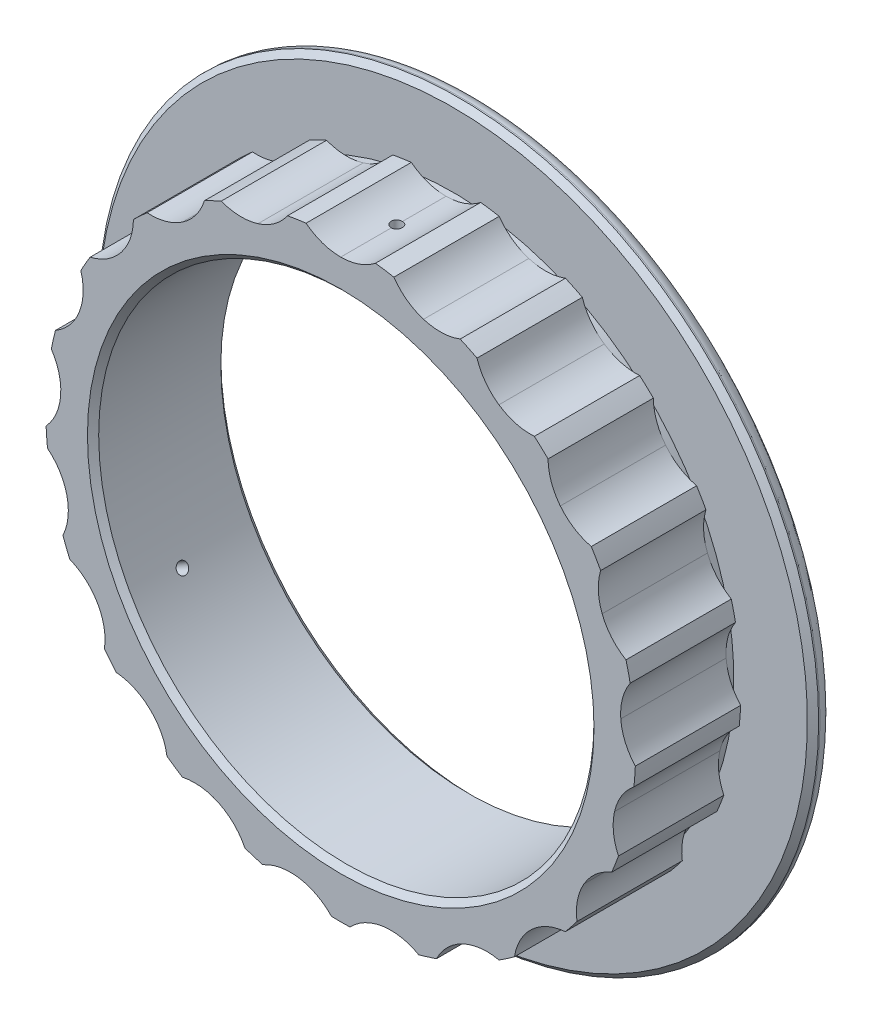
SolidWorks part; units mm, degrees
ref_plane "Front Plane" through (0, 0, 0) normal (0, 0, 1) x (1, 0, 0)
ref_plane "Top Plane" through (0, 0, 0) normal (0, 1, 0) x (1, 0, 0)
ref_plane "Right Plane" through (0, 0, 0) normal (1, 0, 0) x (0, 0, -1)
sketch "Sketch1" plane through (0, 0, 0) normal (0, 0, 1) x (1, 0, 0)
  line L0 (0, -72.8148) -> (0, 10.1901) construction
  circle A0 centre (0, -72.8148) radius 63.5 construction
  circle A1 centre (0, -72.8148) radius 63.5
  circle A2 centre (-22.46, 0) radius 12.7
  circle A3 centre (0, 3.3852) radius 12.7
sketch "Sketch2" plane through (0, 0, 0) normal (0, 0, 1) x (1, 0, 0)
  circle A0 centre (0, -72.8148) radius 56
  circle A1 centre (0, -72.8148) radius 63.5 construction
  circle A2 centre (0, -72.8148) radius 63.5
  dimension "D1" = 112
extrude "Extrude1" add sketch "Sketch2" along normal mid plane 25.4
sketch "Sketch3" plane through (0, 0, 0) normal (0, 0, 1) x (1, 0, 0)
  circle A0 centre (-22.46, 0) radius 12.7 construction
  arc A1 (-18.7166, -12.1358) -> (-12.0204, -7.2323) centre (-22.46, 0) ccw
  circle A2 centre (0, 3.3852) radius 12.7 construction
  arc A3 (-7.8441, -6.6028) -> (0, -9.3148) centre (0, 3.3852) ccw
  arc A5 (-7.8441, -6.6028) -> (-12.0204, -7.2323) centre (0, -72.8148) ccw
  circle A6 centre (0, -72.8148) radius 63.5 construction
  arc A7 (0, -9.3148) -> (-18.7166, -12.1358) centre (0, -72.8148) ccw
  dimension "D1" = 133.35
extrude "Extrude2" add sketch "Sketch3" along normal blind 12.7 and the other way blind 11.1125
pattern_circular "CirPattern1" count 21 over 360 about axis through (0, -72.8148, 0) along (0, 0, 1) of "Extrude2"
sketch "Sketch4" plane through (0, 0, -12.7) normal (0, 0, -1) x (-1, 0, 0)
  circle A0 centre (0, -72.8148) radius 56 construction
  circle A1 centre (0, -72.8148) radius 56
  circle A2 centre (0, -72.8148) radius 81.4
  dimension "D1" = 25.4
extrude "Extrude3" add sketch "Sketch4" along normal blind 4.7625
chamfer "Chamfer1" distance 1.27 angle 45 2 edges at (-56, -72.8148, -17.4625) (56, -72.8148, 12.7)
fillet "Fillet2" radius 3.175 1 edges at (-81.4, -72.8148, -17.4625)
chamfer "Chamfer2" distance 1.27 angle 45 1 edges at (-81.4, -72.8148, -12.7)
sketch "Sketch5" plane through (0, 0, 0) normal (0, 1, 0) x (1, 0, 0)
  circle A0 centre (0, 0) radius 1.27
  dimension "D1" = 2.54
extrude "Cut-Extrude1" cut sketch "Sketch5" against normal up to next
pattern_circular "CirPattern2" count 3 over 360 about axis through (0, -72.8148, 12.7) along (0, 0, -1) of "Cut-Extrude1"
